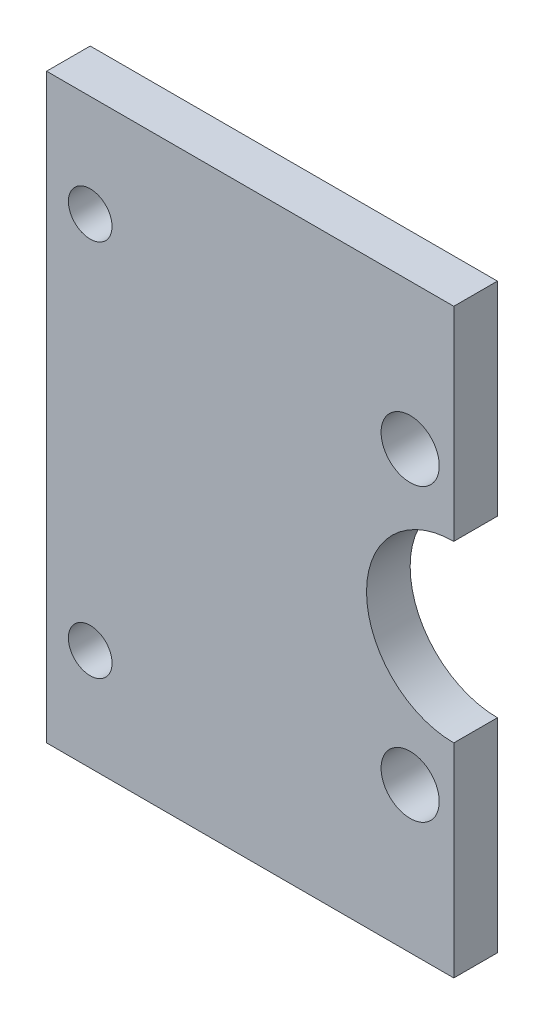
SolidWorks part; units mm, degrees
material "Balsa"
ref_plane "Plan de face" through (0, 0, 0) normal (0, 0, 1) x (1, 0, 0)
ref_plane "Plan de dessus" through (0, 0, 0) normal (0, 1, 0) x (1, 0, 0)
ref_plane "Plan de droite" through (0, 0, 0) normal (1, 0, 0) x (0, 0, -1)
sketch "Esquisse1" plane through (0, 0, 0) normal (0, 0, 1) x (1, 0, 0)
  line L1 (-14, 20) -> (14, 20)
  line L2 (-14, 20) -> (-14, -20)
  line L3 (-14, -20) -> (14, -20)
  line L4 (14, 20) -> (14, -20)
  dimension "D1" = 40
  dimension "D2" = 20
  dimension "D3" = 28
  dimension "D4" = 14
extrude "Boss.-Extru.1" add sketch "Esquisse1" along normal blind 3 contours L1 L4 L3 L2
sketch "Esquisse7" plane through (0, 0, 3) normal (0, 0, 1) x (1, 0, 0)
  circle A0 centre (-11, 13) radius 1.5
  dimension "D1" = 3
  dimension "D2" = 13
  dimension "D3" = 11
extrude "Enlèv. mat.-Extru.6" cut sketch "Esquisse7" against normal blind 5
mirror "Symétrie2" about plane through (0, 0, 0) normal (0, 1, 0) of "Enlèv. mat.-Extru.6"
sketch "Esquisse8" plane through (0, 0, 3) normal (0, 0, 1) x (1, 0, 0)
  circle A0 centre (11, 10) radius 2
  dimension "D1" = 4
  dimension "D2" = 10
  dimension "D3" = 11
extrude "Enlèv. mat.-Extru.7" cut sketch "Esquisse8" against normal blind 10
mirror "Symétrie3" about plane through (0, 0, 0) normal (0, 1, 0) of "Enlèv. mat.-Extru.7"
sketch "Esquisse9" plane through (0, 0, 3) normal (0, 0, 1) x (1, 0, 0)
  line L0 (14, 20) -> (14, -20) construction
  circle A0 centre (14, 0) radius 6
  dimension "D1" = 12
extrude "Enlèv. mat.-Extru.8" cut sketch "Esquisse9" against normal blind 10
